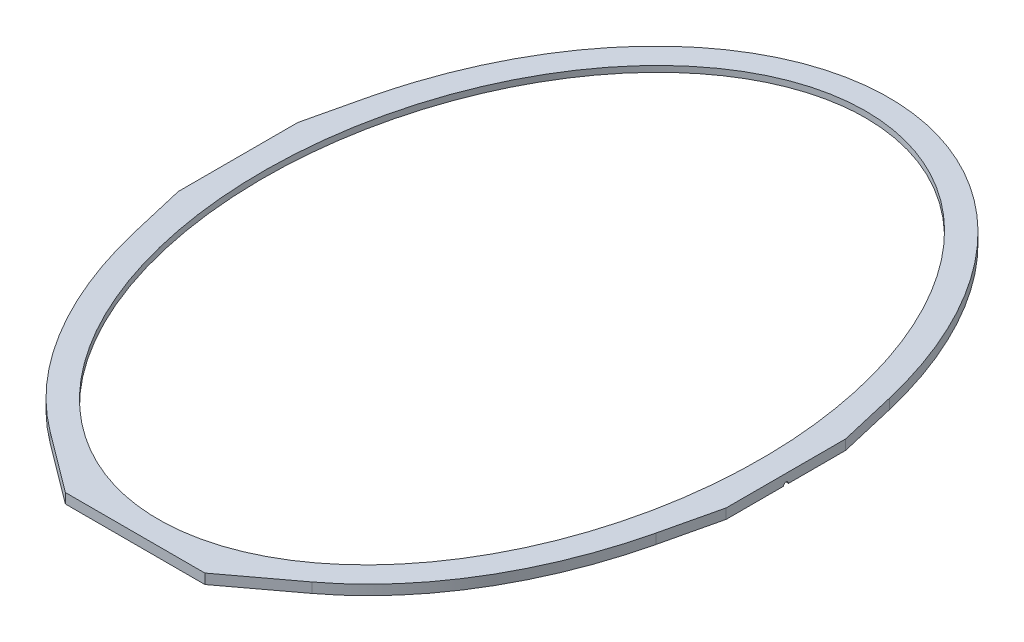
SolidWorks part; units mm, degrees
ref_plane "Front Plane" through (0, 0, 0) normal (0, 0, 1) x (1, 0, 0)
ref_plane "Top Plane" through (0, 0, 0) normal (0, 1, 0) x (1, 0, 0)
ref_plane "Right Plane" through (0, 0, 0) normal (1, 0, 0) x (0, 0, -1)
sketch "Sketch1" plane through (0, 0, 0) normal (0, 1, 0) x (1, 0, 0)
  line L0 (0, 520.2694) -> (0, -520.3963) construction
  line L1 (-478.2136, 0) -> (435.079, 0) construction
  line L2 (-255, 0) -> (-255, 60) construction
  line L3 (-255, 60) -> (-275, 60) construction
  line L4 (-275, 60) -> (-275, -60)
  line L5 (-275, 60) -> (-261.6216, 117.0811)
  line L6 (275, -60) -> (261.6216, -117.0811)
  line L7 (-275, -60) -> (-261.6216, -117.0811)
  line L8 (275, 60) -> (261.6216, 117.0811)
  line L9 (275, 60) -> (275, -60)
  ellipse E0 centre (0, 0) end of major axis (0, 355) minor radius 250
  ellipse E1 centre (0, 0) end of major axis (0, 380) minor radius 275 construction
  ellipse E2 centre (0, 0) end of major axis (0, 378.3034) minor radius 275.1297 (-261.6216, 117.0811) -> (261.6216, 117.0811) cw
  ellipse E4 centre (0, 0) end of major axis (0, -378.3034) minor radius 275.1297 (-261.6216, -117.0811) -> (261.6216, -117.0811) ccw
  point P27 (275, 0)
  point P32 (-275, 0)
  dimension "D1" = 500
  dimension "D2" = 710
  dimension "D3" = 550
  dimension "D4" = 760
  dimension "D5" = 20
  dimension "D7" = 60
extrude "Boss-Extrude1" add sketch "Sketch1" along normal blind 10
sketch "Sketch2" plane through (0, 0, 0) normal (0, -1, 0) x (1, 0, 0)
  line L0 (0, -520.2694) -> (0, 520.3963) construction
  ellipse E0 centre (0, 0) end of major axis (0, 355) minor radius 250
  ellipse E2 centre (0, 0) end of major axis (0, 365) minor radius 260
  dimension "D1" = 10
  dimension "D2" = 10
extrude "Cut-Extrude1" cut sketch "Sketch2" against normal blind 4
sketch "Sketch3" plane through (0, 10, 0) normal (0, 1, 0) x (1, 0, 0)
  line L0 (0, 402.8339) -> (0, -408.949) construction
  line L1 (70, -378.3034) -> (-70, -378.3034)
  line L2 (70, -378.3034) -> (131.4885, -332.3041)
  line L3 (131.4885, -332.3041) -> (0, -361.8757)
  line L4 (-131.4885, -332.3041) -> (0, -361.8757)
  line L5 (-70, -378.3034) -> (-131.4885, -332.3041)
  ellipse E0 centre (0, 0) end of major axis (0, -378.3034) minor radius 275.1297 (-261.6216, -117.0811) -> (261.6216, -117.0811) ccw construction
  point P16 (0, -378.3034)
  dimension "D1" = 70
extrude "Boss-Extrude2" add sketch "Sketch3" against normal blind 10
sketch "Sketch4" plane through (-275, 0, 0) normal (-1, 0, 0) x (0, 0, 1)
  line L0 (-2.5, 0) -> (2.5, 0)
  arc A0 (2.5, 0) -> (-2.5, 0) centre (0, 0) ccw
  dimension "D1" = 5
extrude "Cut-Extrude4" cut sketch "Sketch4" against normal blind 10
sketch "Sketch5" plane through (275, 0, 0) normal (1, 0, 0) x (0, 0, -1)
  line L0 (-60, 0) -> (60, 0) construction
  line L1 (-2.5, 0) -> (2.5, 0)
  arc A0 (2.5, 0) -> (-2.5, 0) centre (0, 0) ccw
  dimension "D1" = 5
extrude "Cut-Extrude5" cut sketch "Sketch5" against normal blind 10
